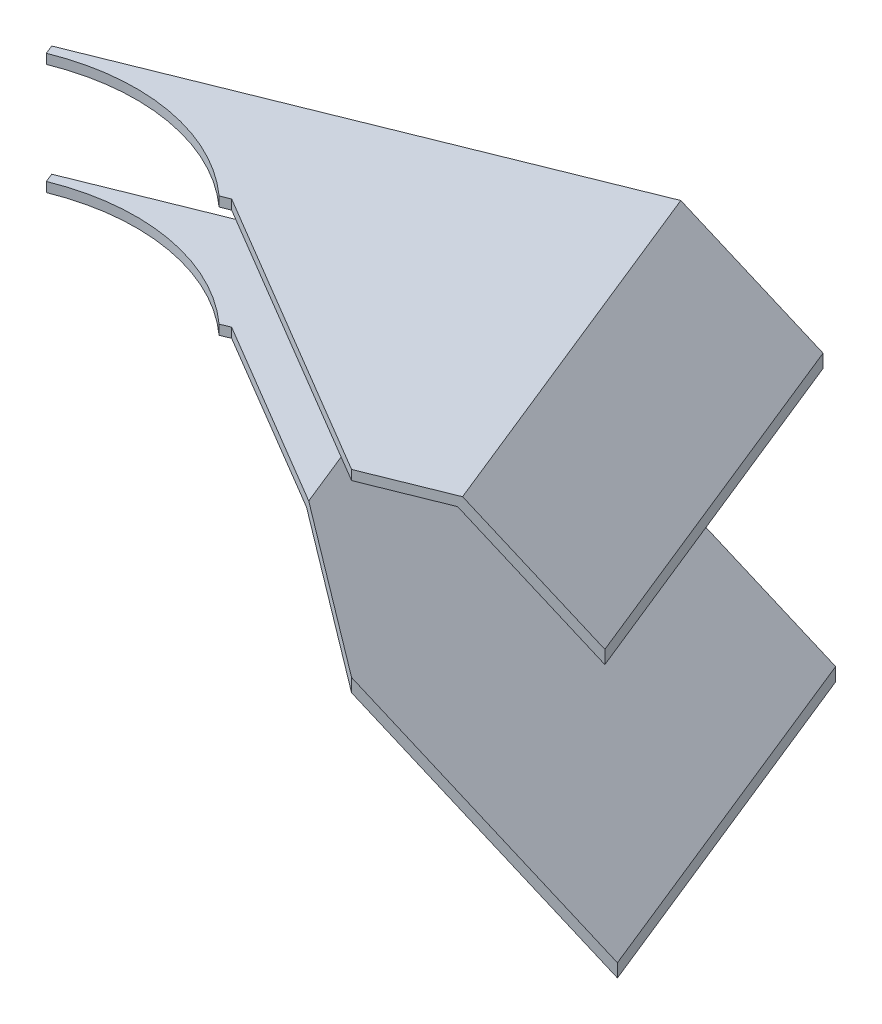
SolidWorks part; units mm, degrees
ref_plane "Front Plane" through (0, 0, 0) normal (0, 0, 1) x (1, 0, 0)
ref_plane "Top Plane" through (0, 0, 0) normal (0, 1, 0) x (1, 0, 0)
ref_plane "Right Plane" through (0, 0, 0) normal (1, 0, 0) x (0, 0, -1)
ref_plane "Plane1" through (72.5959, 0, 180.0551) normal (0.3739, 0, 0.9275) x (0.9275, 0, -0.3739)
sketch "Sketch2" plane through (72.5959, 0, 180.0551) normal (0.3739, 0, 0.9275) x (0.9275, 0, -0.3739)
  line L1 (8042.2097, -13571.4129) -> (8129.9268, -13653.2104) construction
  line L5 (8129.9268, -13653.2104) -> (8129.9268, -13649.1085) construction
  line L9 (8043.3914, -13568.4129) -> (8129.9268, -13649.1085)
  line L10 (-135.6949, 11.606) -> (-8.7543, -106.768) construction
  line L11 (8042.2097, -13571.4129) -> (8129.9268, -13653.2104)
  line L12 (8129.9268, -13653.2104) -> (8129.9268, -13649.1085)
  line L13 (7999.4268, -13568.4129) -> (8001.9268, -13568.4129) construction
  line L14 (7999.4268, -13566.9129) -> (7999.4268, -13569.9129) construction
  line L15 (8043.3914, -13568.4129) -> (8001.9268, -13568.4129)
  line L16 (8001.9268, -13568.4129) -> (8001.9268, -13571.4129)
  line L17 (8001.9268, -13571.4129) -> (8042.2097, -13571.4129)
  dimension "D6" = 3
  dimension "D7" = 3
  dimension "D8" = 2.5
  dimension "D9" = 3
extrude "Boss-Extrude1" add sketch "Sketch2" along normal blind 55 and the other way up to vertex (67.5 mm away)
sketch "Sketch3" plane through (72.5959, 0, 180.0551) normal (0.3739, 0, 0.9275) x (0.9275, 0, -0.3739)
  line L0 (8092.9531, -13533.9221) -> (8126.9268, -13565.6032)
  line L1 (8091.7713, -13536.9221) -> (8126.9268, -13569.7052)
  line L2 (8092.9531, -13533.9221) -> (8001.9268, -13533.9221)
  line L3 (8001.9268, -13533.9221) -> (8001.9268, -13536.9221)
  line L4 (8001.9268, -13536.9221) -> (8091.7713, -13536.9221)
  line L5 (8126.9268, -13565.6032) -> (8126.9268, -13569.7052)
  line L6 (8043.3914, -13568.4129) -> (8001.9268, -13568.4129) construction
  line L8 (8129.9268, -13649.1085) -> (8043.3914, -13568.4129) construction
  line L9 (8001.9268, -13568.4129) -> (8001.9268, -13571.4129) construction
  line L10 (-262.3323, 63.6589) -> (-142.7487, 53.6698) construction
  line L15 (-262.3323, 63.6589) -> (-260.6674, 83.5894) construction
  line L16 (-142.7487, 53.6698) -> (-141.0839, 73.6003) construction
  line L17 (-260.6674, 83.5894) -> (-141.0839, 73.6003) construction
  line L18 (8043.3914, -13568.4129) -> (8129.9268, -13649.1085) construction
  line L19 (8119.6945, -13562.9609) -> (8001.9268, -13539.9221) construction
  line L24 (8119.6945, -13562.9609) -> (8115.8547, -13582.5888) construction
  line L25 (8001.9268, -13539.9221) -> (7998.087, -13559.55) construction
  line L26 (8115.8547, -13582.5888) -> (7998.087, -13559.55) construction
  line L27 (8129.9268, -13621.7619) -> (8042.1644, -13539.9221) construction
  line L29 (8129.9268, -13621.7619) -> (8116.2869, -13636.389) construction
  line L30 (8042.1644, -13539.9221) -> (8028.5244, -13554.5492) construction
  line L31 (8116.2869, -13636.389) -> (8028.5244, -13554.5492) construction
  line L32 (8126.9268, -13650.4129) -> (8126.9268, -13540.3083) construction
  dimension "D1" = 3
  dimension "D2" = 3
  dimension "D3" = 3
  dimension "D4" = 3
  dimension "D5" = 20
  dimension "D6" = 120
  dimension "D7" = 120
  dimension "D8" = 20
  dimension "D9" = 120
  dimension "D10" = 20
  dimension "D11" = 3
extrude "Boss-Extrude2" add sketch "Sketch3" along normal blind 55 and the other way up to vertex (67.5 mm away) separate body
ref_plane "Plane2" through (-2930.6583, -2661.1946, -1735.8748) normal (-0.678, -0.6157, -0.4016) x (-0.7337, 0.6001, 0.3187)
sketch "Sketch6" plane through (-2930.6583, -2661.1946, -1735.8748) normal (-0.678, -0.6157, -0.4016) x (0.7336, -0.6013, -0.3168)
  line L0 (14605.4623, 4343.7105) -> (14689.4932, 4244.5197)
  line L1 (14605.4623, 4343.7105) -> (14423.8189, 4189.8286)
  line L2 (14689.4932, 4244.5197) -> (14507.8498, 4090.6378)
  line L3 (14423.8189, 4189.8286) -> (14507.8498, 4090.6378)
  line L5 (14748.7082, 4174.6218) -> (14602.2303, 4347.5255) construction
  line L6 (14649.9773, 4211.0432) -> (14595.5805, 4164.9602) construction
  line L7 (14617.1861, 4353.6425) -> (14423.8189, 4189.8286) construction
  line L8 (14448.5445, 4160.6423) -> (14421.8797, 4192.1176) construction
extrude "Cut-Extrude1" cut sketch "Sketch6" against normal through all both and the other way through all
sketch "Sketch12" plane through (0, -13568.4129, 0) normal (0, 1, 0) x (1, 0, 0)
  line L0 (7468.7735, 2874.7682) -> (7483.025, 2839.4213)
  line L1 (7483.025, 2839.4213) -> (7480.2426, 2838.2995)
  line L2 (7468.7735, 2874.7682) -> (7413.8873, 2852.6388)
  line L3 (7413.8873, 2852.6388) -> (7415.0091, 2849.8564)
  arc A0 (7415.0091, 2849.8564) -> (7480.2426, 2838.2995) centre (7438.3802, 2791.8906) cw
  dimension "D3" = 62.5
  dimension "D1" = 3
  dimension "D2" = 3
extrude "Boss-Extrude5" add sketch "Sketch12" against normal blind 3
sketch "Sketch13" plane through (0, -13533.9221, 0) normal (0, 1, 0) x (1, 0, 0)
  line L0 (7415.0091, 2849.8564) -> (7413.8873, 2852.6388)
  line L1 (7413.8873, 2852.6388) -> (7468.7735, 2874.7682)
  line L2 (7468.7735, 2874.7682) -> (7483.025, 2839.4213)
  line L3 (7483.025, 2839.4213) -> (7480.2426, 2838.2995)
  arc A0 (7415.0091, 2849.8564) -> (7480.2426, 2838.2995) centre (7438.3802, 2791.8906) cw
extrude "Boss-Extrude6" add sketch "Sketch13" against normal blind 3
